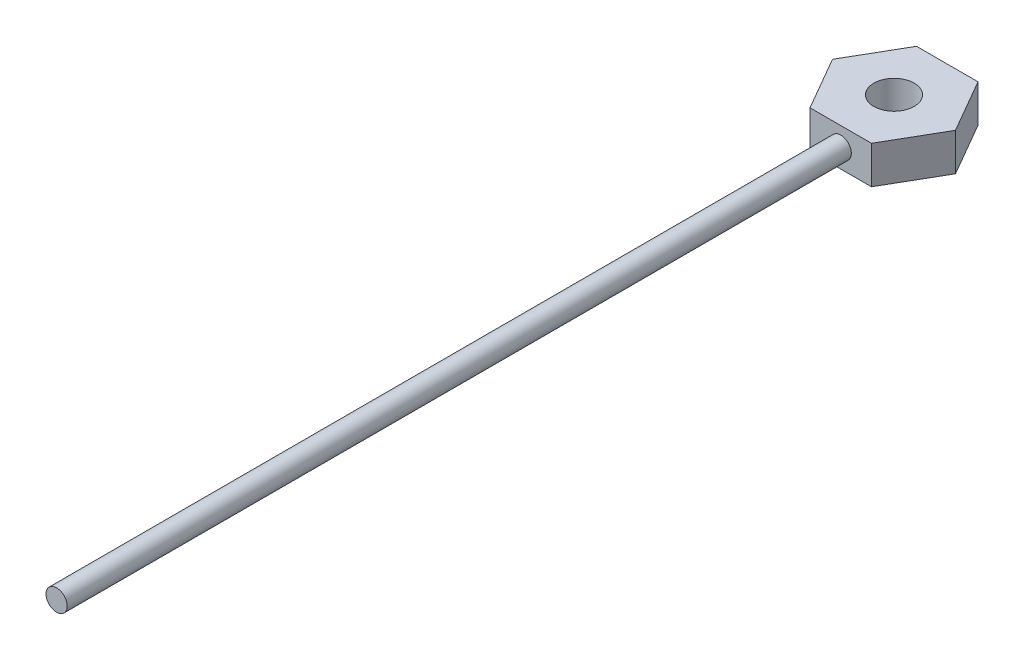
SolidWorks part; units mm, degrees
ref_plane "Alzado" through (0, 0, 0) normal (0, 0, 1) x (1, 0, 0)
ref_plane "Planta" through (0, 0, 0) normal (0, 1, 0) x (1, 0, 0)
ref_plane "Vista lateral" through (0, 0, 0) normal (1, 0, 0) x (0, 0, -1)
sketch "Croquis1" plane through (0, 0, 0) normal (0, 1, 0) x (1, 0, 0)
  line L1 (14.6867, 0) -> (7.3434, 12.7191)
  line L2 (7.3434, 12.7191) -> (-7.3434, 12.7191)
  line L3 (-7.3434, 12.7191) -> (-14.6867, 0)
  line L4 (-14.6867, 0) -> (-7.3434, -12.7191)
  line L5 (-7.3434, -12.7191) -> (7.3434, -12.7191)
  line L6 (7.3434, -12.7191) -> (14.6867, 0)
  circle A0 centre (0, 0) radius 4.825
  circle A1 centre (0, 0) radius 12.7191 construction
  dimension "D1" = 9.65
extrude "Saliente-Extruir1" add sketch "Croquis1" along normal blind 9
sketch "Croquis2" plane through (0, 0, 0) normal (0, 0, 1) x (1, 0, 0)
  circle A0 centre (0, 4.5) radius 2.53
  dimension "D1" = 5.06
extrude "Saliente-Extruir2" add sketch "Croquis2" along normal blind 200
sketch "Croquis3" plane through (0, 0, 0) normal (0, 1, 0) x (1, 0, 0)
  circle A0 centre (0, 0) radius 4.825
extrude "Cortar-Extruir1" cut sketch "Croquis3" along normal blind 29 and the other way blind 67
